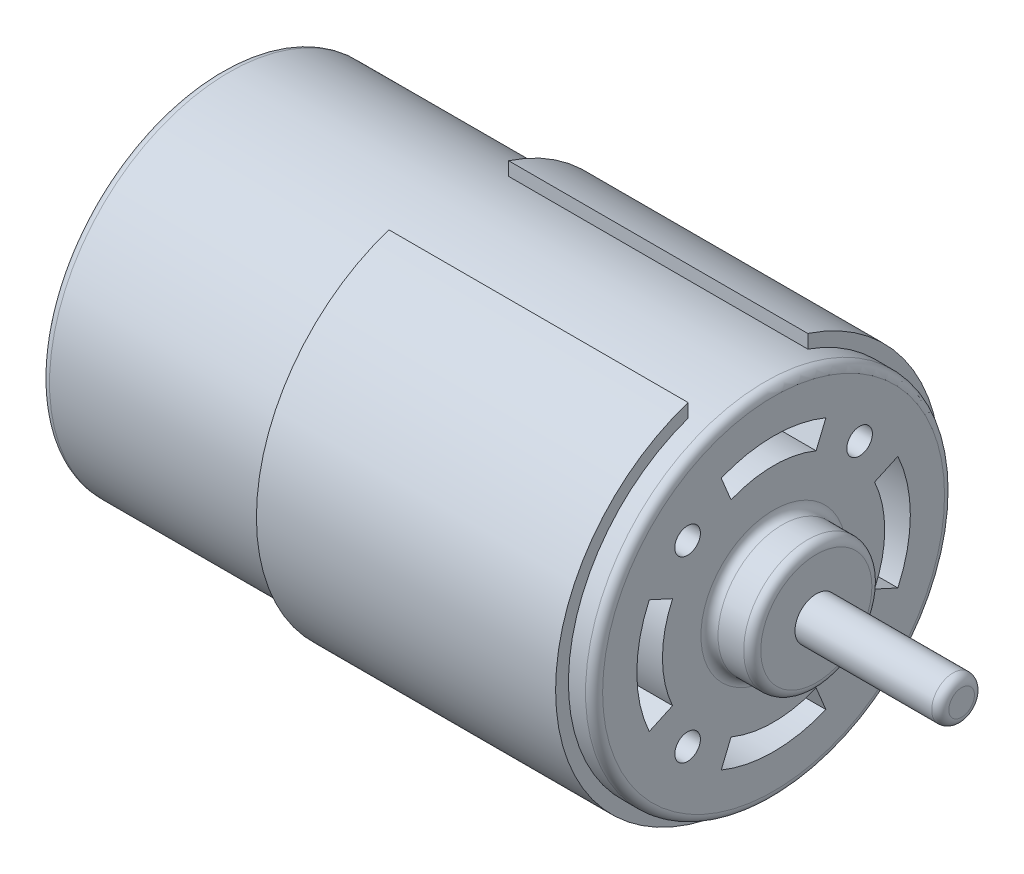
SolidWorks part; units mm, degrees
ref_plane "Front Plane" through (0, 0, 0) normal (0, 0, 1) x (1, 0, 0)
ref_plane "Top Plane" through (0, 0, 0) normal (0, 1, 0) x (1, 0, 0)
ref_plane "Right Plane" through (0, 0, 0) normal (1, 0, 0) x (0, 0, -1)
sketch "Sketch1" plane through (0, 0, 0) normal (1, 0, 0) x (0, 0, -1)
  circle A0 centre (0, 0) radius 21
  dimension "D1" = 42
extrude "Boss-Extrude1" add sketch "Sketch1" along normal blind 26.7
sketch "Sketch2" plane through (26.7, 0, 0) normal (1, 0, 0) x (0, 0, -1)
  circle A0 centre (0, 0) radius 22.5
  dimension "D1" = 45
extrude "Boss-Extrude2" add sketch "Sketch2" along normal blind 35
sketch "Sketch3" plane through (61.7, 0, 0) normal (1, 0, 0) x (0, 0, -1)
  circle A0 centre (0, 0) radius 21
  dimension "D1" = 42
extrude "Boss-Extrude3" add sketch "Sketch3" along normal blind 3
sketch "Sketch4" plane through (64.7, 0, 0) normal (1, 0, 0) x (0, 0, -1)
  circle A0 centre (0, 0) radius 7.5
  dimension "D1" = 15
extrude "Boss-Extrude4" add sketch "Sketch4" along normal blind 5
sketch "Sketch5" plane through (69.7, 0, 0) normal (1, 0, 0) x (0, 0, -1)
  circle A0 centre (0, 0) radius 2.5
  dimension "D1" = 5
extrude "Boss-Extrude5" add sketch "Sketch5" along normal blind 17
sketch3d "3DSketch1" plane through (0, 0, 0) normal (0, 0, 1) x (1, 0, 0)
  dimension "D1" = 30
sketch "Sketch6" plane through (0, 30, 0) normal (0, 1, 0) x (1, 0, 0)
  line L0 (0, 0) -> (93.1265, 0) construction
  line L1 (44.2, -22.5) -> (44.2, 22.5) construction
  line L2 (26.7, -22.5) -> (61.7, -22.5) construction
  line L3 (61.7, 22.5) -> (26.7, 22.5) construction
  line L4 (26.7, -7) -> (61.7, -7)
  line L5 (26.7, 7) -> (61.7, 7)
  line L6 (61.7, -7) -> (61.7, 7)
  line L7 (26.7, -7) -> (26.7, 7)
  line L8 (61.7, -22.5) -> (61.7, 22.5) construction
  line L9 (0, -7) -> (93.1265, -7) construction
  line L10 (0, 7) -> (93.1265, 7) construction
  line L11 (26.7, -22.5) -> (26.7, 22.5) construction
  dimension "D1" = 7
  dimension "D2" = 7
  dimension "D3" = 17.5
  dimension "D4" = 17.5
extrude "Cut-Extrude1" cut sketch "Sketch6" against normal up to surface (10.201 mm away)
fillet "Fillet1" radius 1 4 edges at (0, 0, -21) (64.7, 0, -7.5) (69.7, 0, -7.5) (64.7, 0, -21)
sketch "Sketch7" plane through (0, 0, 0) normal (-1, 0, 0) x (0, 0, 1)
  circle A0 centre (0, 0) radius 7.5
  dimension "D1" = 15
extrude "Boss-Extrude6" add sketch "Sketch7" along normal blind 5
sketch "Sketch8" plane through (-5, 0, 0) normal (-1, 0, 0) x (0, 0, 1)
  circle A0 centre (0, 0) radius 2.5
  dimension "D1" = 5
extrude "Boss-Extrude7" add sketch "Sketch8" along normal blind 5
chamfer "Chamfer1" distance 2 angle 45 1 edges at (-5, 0, 7.5)
fillet "Fillet2" radius 1 4 edges at (86.7, 0, -2.5) (-10, 0, 2.5) (0, 0, -7.5) (-3, 0, 7.5)
sketch "Sketch9" plane through (64.7, 0, 0) normal (1, 0, 0) x (0, 0, -1)
  line L0 (0, 0) -> (0, 13)
  line L1 (-10.0599, 10.4427) -> (10.0599, 10.4427) construction
  line L2 (-10.0599, 10.4427) -> (-10.0599, -10.4427) construction
  line L3 (-10.0599, -10.4427) -> (10.0599, -10.4427) construction
  line L4 (10.0599, 10.4427) -> (10.0599, -10.4427) construction
  line L5 (-10.0599, 10.4427) -> (10.0599, -10.4427) construction
  line L6 (-10.0599, -10.4427) -> (10.0599, 10.4427) construction
  line L7 (0, 0) -> (-13, 0)
  line L8 (0, 0) -> (13, 0)
  line L9 (0, 0) -> (0, -13)
  line L10 (0, 0) -> (-7.6537, 18.4776)
  line L11 (0, 0) -> (7.6537, 18.4776)
  line L12 (0, 0) -> (18.179, 8.3381)
  line L13 (0, 0) -> (18.179, -8.3381)
  line L14 (0, 0) -> (7.6537, -18.4776)
  line L15 (0, 0) -> (-7.6537, -18.4776)
  line L16 (0, 0) -> (-18.179, -8.3381)
  line L17 (0, 0) -> (-18.179, 8.3381)
  line L18 (0, 16) -> (0, 20)
  line L19 (-16, 0) -> (-20, 0)
  line L20 (0, -16) -> (0, -20)
  line L21 (16, 0) -> (20, 0)
  circle A0 centre (-10.0599, 10.4427) radius 1.5
  circle A1 centre (10.0599, 10.4427) radius 1.5
  circle A2 centre (10.0599, -10.4427) radius 1.5
  circle A3 centre (-10.0599, -10.4427) radius 1.5
  arc A4 (-5.5489, 13.3963) -> (-8.9272, 11.4261) centre (0, 0) ccw
  circle A5 centre (0, 0) radius 16
  circle A6 centre (0, 0) radius 13
  circle A7 centre (0, 0) radius 20 construction
  circle A8 centre (0, 0) radius 14.5 construction
  arc A9 (-13.1798, -6.0451) -> (-11.0849, -9.3475) centre (0, 0) ccw
  arc A10 (5.5489, -13.3963) -> (8.9272, -11.4261) centre (0, 0) ccw
  arc A11 (13.1798, 6.0451) -> (11.0849, 9.3475) centre (0, 0) ccw
  arc A12 (11.0849, -9.3475) -> (13.1798, -6.0451) centre (0, 0) ccw
  arc A13 (-8.9272, -11.4261) -> (-5.5489, -13.3963) centre (0, 0) ccw
  arc A14 (8.9272, 11.4261) -> (5.5489, 13.3963) centre (0, 0) ccw
  arc A15 (-11.0849, 9.3475) -> (-13.1798, 6.0451) centre (0, 0) ccw
  point P0 (0, 0)
  point P6 (-10.0599, 0)
  dimension "D3" = 3
  dimension "D4" = 3
  dimension "D5" = 3
  dimension "D6" = 3
  dimension "D1" = 29
  dimension "D2" = 10.0599
  dimension "D9" = 22.5
  dimension "D7" = 1.5
  dimension "D8" = 1.5
extrude "Cut-Extrude2" cut sketch "Sketch9" against normal blind 10 contours A0 | A6 L11 A5 L10 | A1 | A6 L13 A5 L12 | A2 | A6 L15 A5 L14 | A3 | A6 L17 A5 L16
